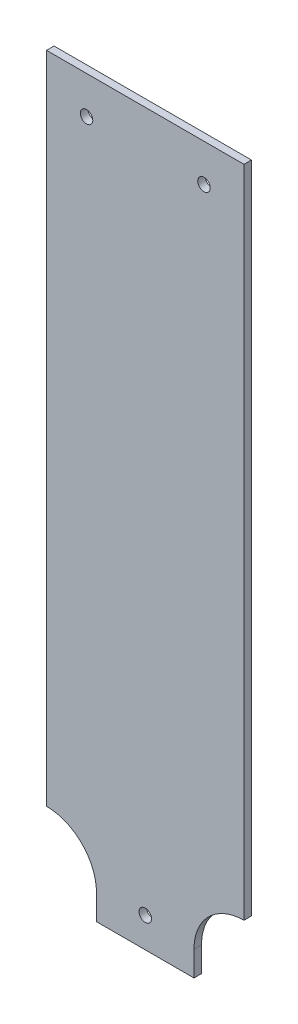
SolidWorks part; units mm, degrees
ref_plane "Face" through (0, 0, 0) normal (0, 0, 1) x (1, 0, 0)
ref_plane "Dessus" through (0, 0, 0) normal (0, 1, 0) x (1, 0, 0)
ref_plane "Droite" through (0, 0, 0) normal (1, 0, 0) x (0, 0, -1)
sketch "Esquisse1" plane through (0, 0, 0) normal (0, 0, 1) x (1, 0, 0)
  line L0 (0, 0) -> (0, 292) construction
  line L1 (39.5, 292) -> (-39.5, 292)
  line L2 (-39.5, 292) -> (-39.5, 30)
  line L3 (19.5, 0) -> (-19.5, 0)
  line L4 (-19.5, 0) -> (-19.5, 10)
  line L5 (-39.5, 30) -> (-39.5, 60) construction
  line L6 (39.5, 30) -> (39.5, 60) construction
  line L7 (19.5, 0) -> (19.5, 10)
  line L8 (39.5, 292) -> (39.5, 30)
  arc A0 (-39.5, 30) -> (-19.5, 10) centre (-39.5, 10) cw
  arc A1 (39.5, 30) -> (19.5, 10) centre (39.5, 10) ccw
  circle A2 centre (-23.5, 277) radius 2.5
  circle A3 centre (23.5, 277) radius 2.5
  circle A4 centre (0, 12) radius 2.5
  dimension "D3" = 20
  dimension "D5" = 15
  dimension "D6" = 16
  dimension "D7" = 5
  dimension "D8" = 12
  dimension "D9" = 5
  dimension "D1" = 292
  dimension "D2" = 39.5
  dimension "D4" = 30
extrude "Extrusion1" add sketch "Esquisse1" along normal blind 3
